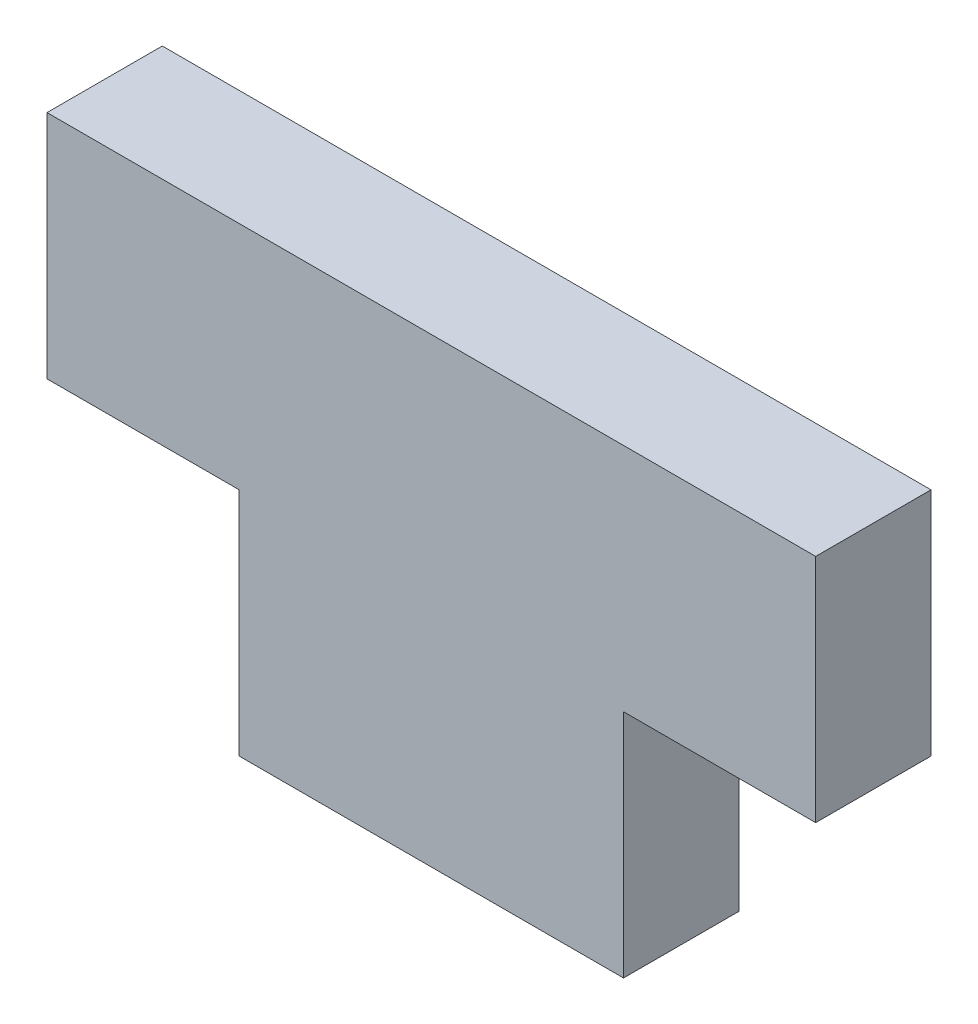
SolidWorks part; units mm, degrees
ref_plane "Plan de face" through (0, 0, 0) normal (0, 0, 1) x (1, 0, 0)
ref_plane "Plan de dessus" through (0, 0, 0) normal (0, 1, 0) x (1, 0, 0)
ref_plane "Plan de droite" through (0, 0, 0) normal (1, 0, 0) x (0, 0, -1)
sketch "Esquisse1" plane through (0, 0, 0) normal (0, 0, 1) x (1, 0, 0)
  line L0 (-50, 0) -> (50, 0)
other "Elément mécano-soudé1"
ref_plane "Plan1" through (-50, 0, 0) normal (1, 0, 0) x (0, 1, 0)
sketch "plat" plane through (-50, 0, 0) normal (1, 0, 0) x (0, 1, 0)
  line L0 (-30, 0) -> (30, 0) construction
  line L1 (-30, 7.5) -> (30, 7.5)
  line L2 (-30, 7.5) -> (-30, -7.5)
  line L3 (-30, -7.5) -> (30, -7.5)
  line L4 (30, 7.5) -> (30, -7.5)
  line L5 (0, 7.5) -> (0, -7.5) construction
  point P8 (0, 0)
  dimension "B" = 60
  dimension "A" = 15
sketch "Esquisse2" plane through (0, 0, 7.5) normal (0, 0, 1) x (1, 0, 0)
  line L0 (-50, 30) -> (-50, -30) construction
  line L2 (-50, 0) -> (-25, 0)
  line L3 (-50, 0) -> (-50, -30)
  line L4 (-50, -30) -> (-25, -30)
  line L6 (-25, 0) -> (-25, -30)
  line L7 (50, -30) -> (-50, -30) construction
  line L8 (50, 30) -> (50, -30) construction
  line L9 (50, 0) -> (25, 0)
  line L10 (50, 0) -> (50, -30)
  line L11 (50, -30) -> (25, -30)
  line L12 (25, 0) -> (25, -30)
  dimension "D1" = 50
  dimension "D2" = 25
  dimension "D3" = 25
extrude "Enlèv. mat.-Extru.1" cut sketch "Esquisse2" against normal blind 20
